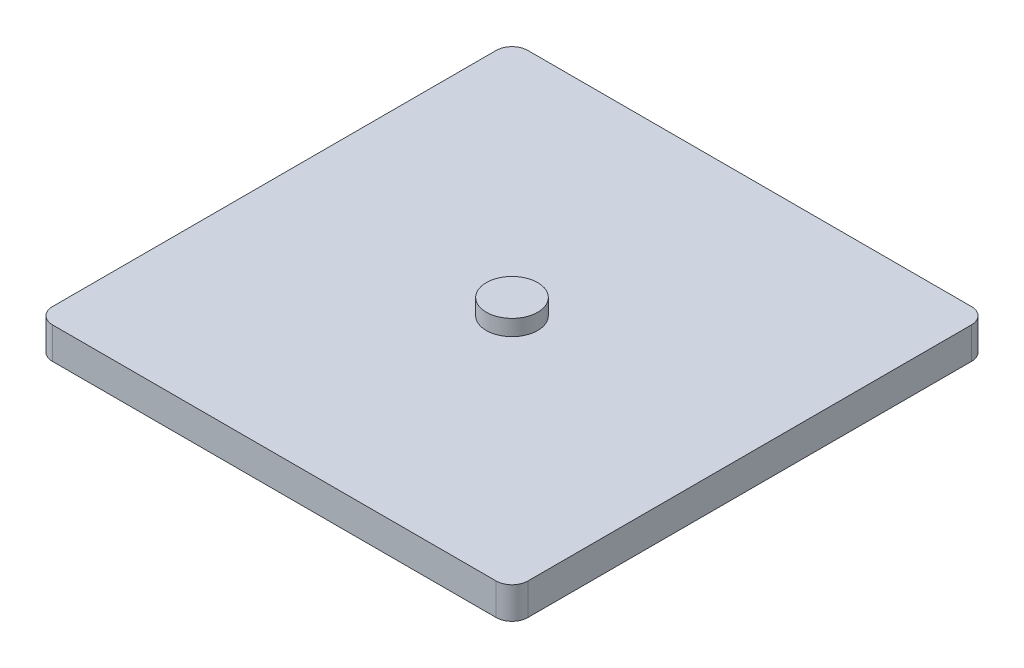
SolidWorks part; units mm, degrees
ref_plane "Front Plane" through (0, 0, 0) normal (0, 0, 1) x (1, 0, 0)
ref_plane "Top Plane" through (0, 0, 0) normal (0, 1, 0) x (1, 0, 0)
ref_plane "Right Plane" through (0, 0, 0) normal (1, 0, 0) x (0, 0, -1)
sketch "Sketch1" plane through (0, 0, 0) normal (0, 1, 0) x (1, 0, 0)
  line L1 (-150, 150) -> (150, 150)
  line L2 (-150, 150) -> (-150, -150)
  line L3 (-150, -150) -> (150, -150)
  line L4 (150, 150) -> (150, -150)
  line L5 (-150, 150) -> (150, -150) construction
  line L6 (-150, -150) -> (150, 150) construction
  point P0 (0, 0)
  dimension "D1" = 300
  dimension "D2" = 300
extrude "Boss-Extrude1" add sketch "Sketch1" along normal blind 20
fillet "Fillet1" radius 10 4 edges at (-150, 10, -150) (150, 10, -150) (150, 10, 150) (-150, 10, 150)
sketch "Sketch2" plane through (0, 20, 0) normal (0, 1, 0) x (1, 0, 0)
  circle A0 centre (0, 0) radius 16.2225
extrude "Boss-Extrude2" add sketch "Sketch2" along normal blind 10
